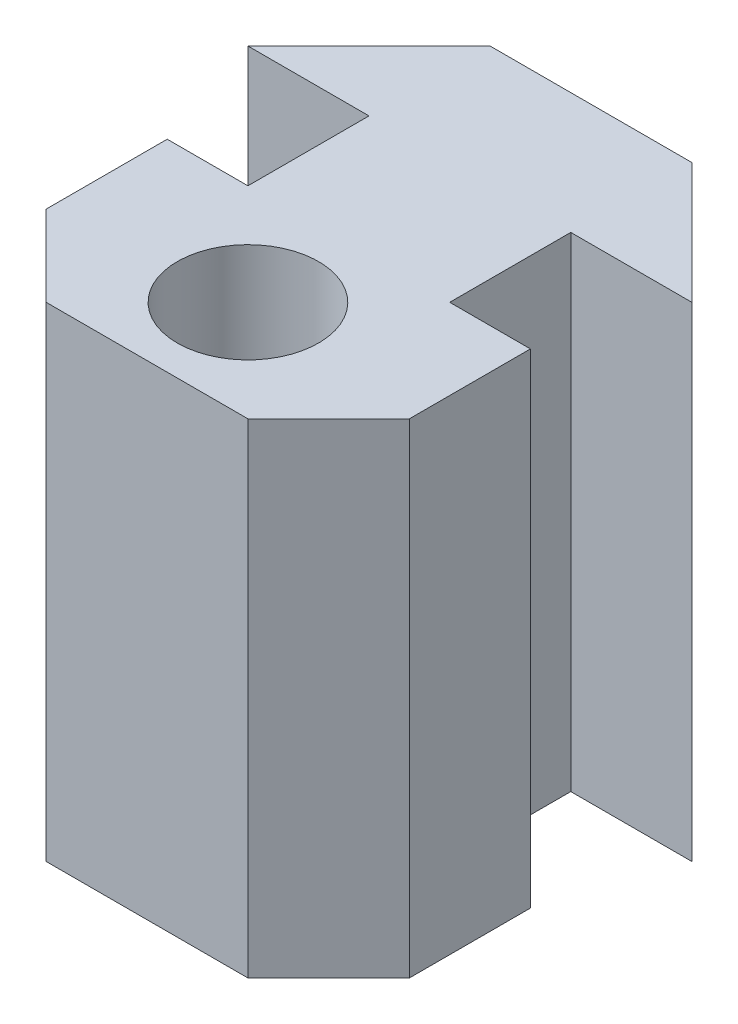
SolidWorks part; units mm, degrees
ref_plane "Plan de face" through (0, 0, 0) normal (1, 0, 0) x (0, 1, 0)
ref_plane "Plan de dessus" through (0, 0, 0) normal (0, 0, 1) x (0, 1, 0)
ref_plane "Plan de droite" through (0, 0, 0) normal (0, 1, 0) x (-1, 0, 0)
sketch "Esquisse1" plane through (0, 0, 0) normal (0, 1, 0) x (-1, 0, 0)
  line L0 (-5.5, 3) -> (-2.5, 0)
  line L2 (-2.5, 6) -> (-2.5, 3)
  line L4 (2.5, 6) -> (2.5, 3)
  line L5 (-2.5, 3) -> (-5.5, 3)
  line L9 (2.5, 3) -> (5.5, 3)
  line L13 (5.5, 3) -> (2.5, 0)
  line L14 (2.5, 6) -> (4.5, 6)
  line L19 (-4.5, 11) -> (4.5, 11)
  line L20 (-4.5, 11) -> (-4.5, 6)
  line L21 (-4.5, 6) -> (-2.5, 6)
  line L22 (4.5, 11) -> (4.5, 6)
  line L23 (-2.5, 0) -> (2.5, 0)
  circle A0 centre (0, 8.5) radius 1.75
  dimension "D7" = 3.5
  dimension "D8" = 2.5
  dimension "D9" = 4.5
  dimension "D1" = 5
  dimension "D2" = 3
  dimension "D3" = 3
  dimension "D4" = 11
  dimension "D5" = 2
  dimension "D6" = 5
extrude "Boss.-Extru.1" add sketch "Esquisse1" along normal blind 12
chamfer "Chanfrein1" distance 2 angle 45 2 edges at (-4.5, 6, 11) (4.5, 6, 11)
